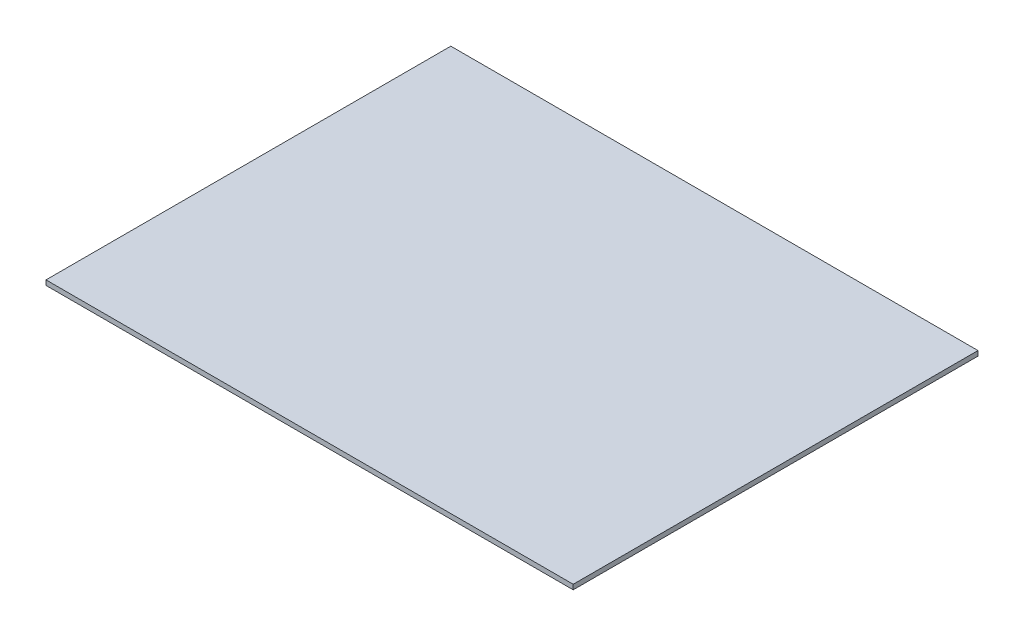
SolidWorks part; units mm, degrees
ref_plane "Спереди" through (0, 0, 0) normal (0, 0, 1) x (1, 0, 0)
ref_plane "Сверху" through (0, 0, 0) normal (0, 1, 0) x (1, 0, 0)
ref_plane "Справа" through (0, 0, 0) normal (1, 0, 0) x (0, 0, -1)
sketch "Эскиз1" plane through (0, 0, 0) normal (0, 1, 0) x (1, 0, 0)
  line L1 (-217.5, -167) -> (217.5, -167)
  line L2 (-217.5, -167) -> (-217.5, 167)
  line L3 (-217.5, 167) -> (217.5, 167)
  line L4 (217.5, -167) -> (217.5, 167)
  line L5 (-217.5, -167) -> (217.5, 167) construction
  line L6 (-217.5, 167) -> (217.5, -167) construction
  point P0 (0, 0)
  dimension "D1" = 334
  dimension "D2" = 435
extrude "Бобышка-Вытянуть1" add sketch "Эскиз1" along normal blind 4
